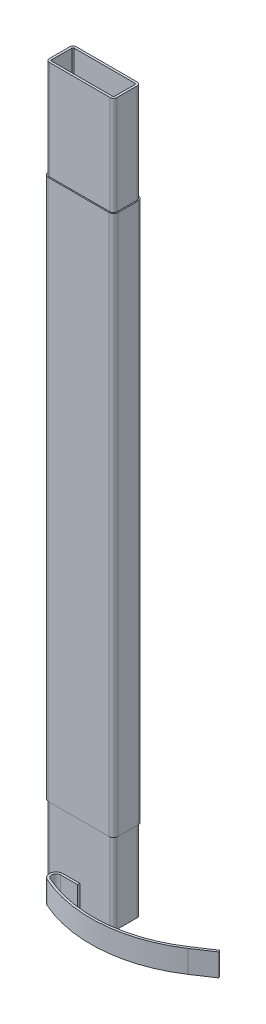
SolidWorks part; units mm, degrees
material "Chrome Stainless Steel"
ref_plane "Front Plane" through (0, 0, 0) normal (0, 0, 1) x (1, 0, 0)
ref_plane "Top Plane" through (0, 0, 0) normal (0, 1, 0) x (1, 0, 0)
ref_plane "Right Plane" through (0, 0, 0) normal (1, 0, 0) x (0, 0, -1)
sketch "Sketch1" plane through (0, 0, 0) normal (0, 1, 0) x (1, 0, 0)
  line L0 (-108.4593, 0) -> (108.4593, 0) construction
  line L1 (-1.35, 0.6) -> (1.35, 0.6)
  line L2 (-1.5, 0.45) -> (-1.5, -0.45)
  line L3 (-1.35, -0.6) -> (1.35, -0.6)
  line L4 (1.5, 0.45) -> (1.5, -0.45)
  line L5 (0, -1.2642) -> (0, 1.2642) construction
  arc A0 (-1.5, -0.45) -> (-1.35, -0.6) centre (-1.35, -0.45) ccw
  arc A1 (-1.5, 0.45) -> (-1.35, 0.6) centre (-1.35, 0.45) cw
  arc A2 (1.5, 0.45) -> (1.35, 0.6) centre (1.35, 0.45) ccw
  arc A3 (1.5, -0.45) -> (1.35, -0.6) centre (1.35, -0.45) cw
  point P12 (-1.5, 0.6)
  point P15 (1.5, 0.6)
  dimension "D5" = 0.15
  dimension "D1" = 3
  dimension "D2" = 1.2
  dimension "D3" = 0.6
  dimension "D4" = 1.5
extrude "Extrude-Thin1" add sketch "Sketch1" along normal blind 30.4 and the other way blind 1.6 thin
ref_plane "Plane2" through (0, 14, 0) normal (0, 1, 0) x (-1, 0, 0)
ref_plane "Plane3" through (0, -0.5, 0) normal (0, 1, 0) x (-1, 0, 0)
sketch "Sketch2" plane through (0, 14, 0) normal (0, 1, 0) x (-1, 0, 0)
  line L0 (1.5, -0.45) -> (1.5, 0.45) construction
  line L1 (-1.35, 0.6) -> (1.35, 0.6)
  line L2 (-1.5, 0.45) -> (-1.5, -0.45)
  line L3 (-1.35, -0.6) -> (1.35, -0.6)
  line L4 (1.5, 0.45) -> (1.5, -0.45)
  line L5 (1.35, 0.6) -> (-1.35, 0.6) construction
  line L6 (-1.5, 0.45) -> (-1.5, -0.45) construction
  line L7 (-1.35, -0.6) -> (1.35, -0.6) construction
  arc A0 (-1.5, 0.45) -> (-1.35, 0.6) centre (-1.35, 0.45) cw
  arc A1 (1.35, 0.6) -> (1.5, 0.45) centre (1.35, 0.45) cw
  arc A2 (1.35, -0.6) -> (1.5, -0.45) centre (1.35, -0.45) ccw
  arc A3 (-1.5, -0.45) -> (-1.35, -0.6) centre (-1.35, -0.45) ccw
  point P12 (-100001.35, -0.6)
  dimension "D1" = 0.15
extrude "Extrude-Thin2" add sketch "Sketch2" along normal mid plane 24 thin thin type one direction wall 0.05
sketch "Sketch3" plane through (0, -0.5, 0) normal (0, -1, 0) x (1, 0, 0)
  line L0 (108.4593, 0) -> (-108.4593, 0) construction
  line L1 (0, -55) -> (0, 55) construction
  line L2 (0, 0.6) -> (-0.75, 0.6)
  line L3 (-1.35, 0.6) -> (1.35, 0.6) construction
  line L4 (4.9, 0.7023) -> (5.7336, 0.15)
  circle A0 centre (5.1, 0) radius 0.475 construction
  arc A1 (-0.75, 0.6) -> (-0.8729, 1.1737) centre (-0.75, 0.9) cw
  arc A2 (-0.8729, 1.1737) -> (4.9, 0.7023) centre (1.5859, -4.2994) cw
  dimension "D1" = 0.95
  dimension "D3" = 0.3
  dimension "D4" = 6
  dimension "D2" = 5.1
  dimension "D5" = 0.75
  dimension "D6" = 1
  dimension "D7" = 0.2
extrude "Extrude-Thin3" add sketch "Sketch3" along normal blind 1 thin
